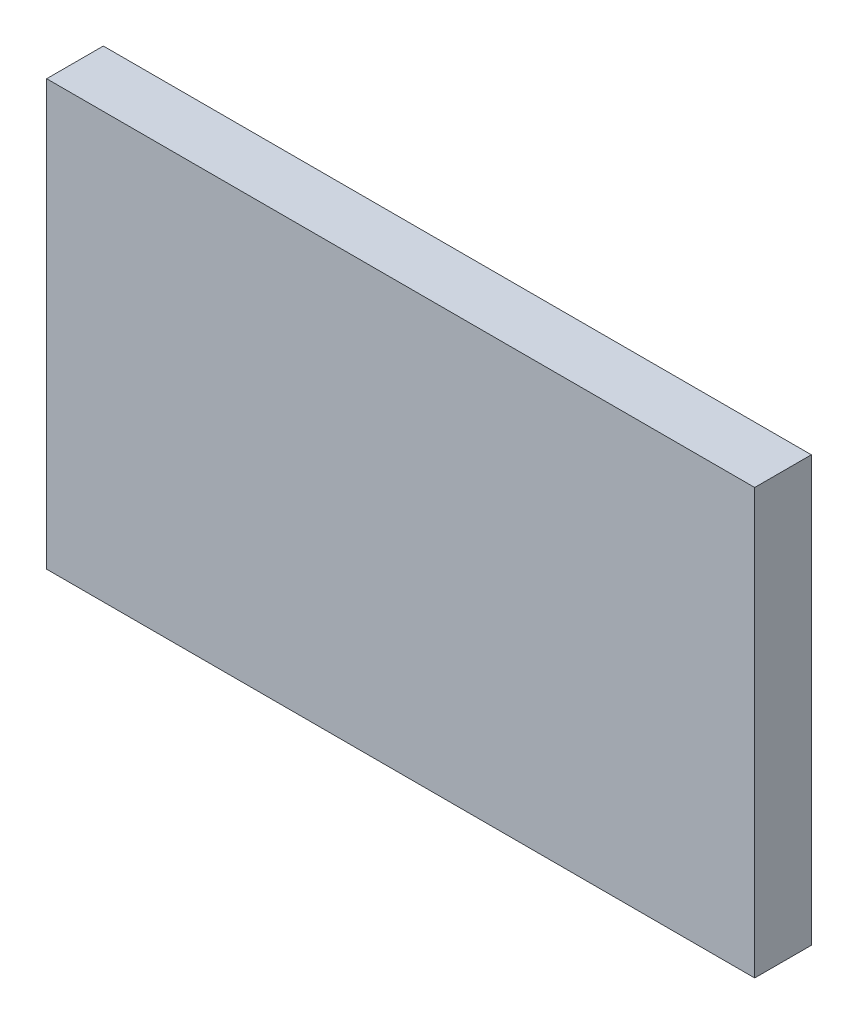
SolidWorks part; units mm, degrees
ref_plane "Front Plane" through (0, 0, 0) normal (0, 0, 1) x (1, 0, 0)
ref_plane "Top Plane" through (0, 0, 0) normal (0, 1, 0) x (1, 0, 0)
ref_plane "Right Plane" through (0, 0, 0) normal (1, 0, 0) x (0, 0, -1)
sketch "Sketch2" plane through (0, 0, 0) normal (0, 0, 1) x (1, 0, 0)
  line L1 (0, 0) -> (200, 0)
  line L2 (0, 0) -> (0, 120)
  line L3 (0, 120) -> (200, 120)
  line L4 (200, 0) -> (200, 120)
  dimension "D1" = 120
  dimension "D2" = 200
extrude "Boss-Extrude1" add sketch "Sketch2" along normal blind 16
